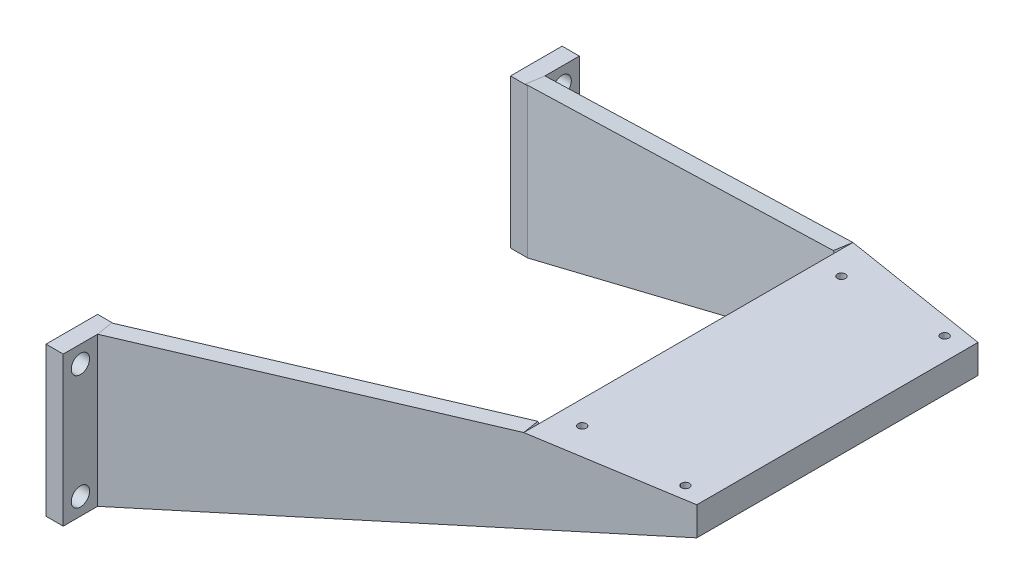
SolidWorks part; units mm, degrees
ref_plane "前视基准面" through (0, 0, 0) normal (0, 0, 1) x (1, 0, 0)
ref_plane "上视基准面" through (0, 0, 0) normal (0, 1, 0) x (1, 0, 0)
ref_plane "右视基准面" through (0, 0, 0) normal (1, 0, 0) x (0, 0, -1)
sketch "草图1" plane through (0, 0, 0) normal (1, 0, 0) x (0, 0, -1)
  line L0 (-2.8172, 6.9162) -> (-2.8172, -19.0838) construction
  line L1 (-5.8172, 6.9162) -> (0.1828, 6.9162)
  line L2 (-5.8172, 6.9162) -> (-5.8172, -19.0838)
  line L3 (-5.8172, -19.0838) -> (0.1828, -19.0838)
  line L4 (0.1828, 6.9162) -> (0.1828, -19.0838)
  line L5 (-44.8172, 16.944) -> (-44.8172, -30.3797) construction
  line L10 (-5.8172, 6.9162) -> (-5.8172, -19.0838)
  line L11 (0.1828, 6.9162) -> (0.1828, -19.0838)
  line L12 (-86.8172, 6.9162) -> (-86.8172, -19.0838) construction
  line L13 (-89.8172, 6.9162) -> (-89.8172, -19.0838)
  line L14 (-83.8172, 6.9162) -> (-83.8172, -19.0838)
  line L15 (-89.8172, 6.9162) -> (-89.8172, -19.0838)
  line L16 (-83.8172, -19.0838) -> (-89.8172, -19.0838)
  line L17 (-83.8172, 6.9162) -> (-83.8172, -19.0838)
  line L18 (-83.8172, 6.9162) -> (-89.8172, 6.9162)
  circle A0 centre (-2.8172, 3.9162) radius 1.6
  circle A1 centre (-2.8172, -16.0838) radius 1.6
  circle A2 centre (-86.8172, -16.0838) radius 1.6
  circle A3 centre (-86.8172, 3.9162) radius 1.6
  dimension "D2" = 3.2
  dimension "D3" = 3.2
  dimension "D1" = 20
  dimension "D4" = 6
  dimension "D5" = 3
  dimension "D6" = 3
  dimension "D7" = 42
extrude "凸台-拉伸1" add sketch "草图1" along normal blind 3 contours L4 L1 L2 L3 A1 A0 | L14 L18 L13 L16 A2 A3
ref_plane "基准面1" through (90, 0, 0) normal (-1, 0, 0) x (0, 0, 1)
sketch "草图10" plane through (3, 0, 0) normal (1, 0, 0) x (0, 0, -1)
  line L0 (-5.8172, -19.0838) -> (0.1828, -19.0838) construction
  line L1 (-5.8172, 6.9162) -> (-8.8172, 6.9162)
  line L2 (-5.8172, 6.9162) -> (-5.8172, -19.0838)
  line L3 (-5.8172, -19.0838) -> (-8.8172, -19.0838)
  line L4 (-8.8172, 6.9162) -> (-8.8172, -19.0838)
  dimension "D1" = 3
sketch "草图11" plane through (90, 0, 0) normal (-1, 0, 0) x (0, 0, 1)
  line L0 (5.8172, 6.9162) -> (8.8172, 6.9162) construction
  line L1 (19.8172, 18.9162) -> (22.8172, 18.9162)
  line L2 (19.8172, 18.9162) -> (19.8172, 8.9162)
  line L3 (19.8172, 8.9162) -> (22.8172, 8.9162)
  line L4 (22.8172, 18.9162) -> (22.8172, 8.9162)
  line L5 (8.8172, 6.9162) -> (8.8172, -19.0838) construction
  dimension "D1" = 12
  dimension "D2" = 11
  dimension "D3" = 10
  dimension "D4" = 3
loft "放样4" add profiles "草图11", "草图10"
sketch "草图12" plane through (3, 0, 0) normal (1, 0, 0) x (0, 0, -1)
  line L0 (-83.8172, -19.0838) -> (-89.8172, -19.0838) construction
  line L1 (-83.8172, 6.9162) -> (-80.8172, 6.9162)
  line L2 (-83.8172, 6.9162) -> (-83.8172, -19.0838)
  line L3 (-83.8172, -19.0838) -> (-80.8172, -19.0838)
  line L4 (-80.8172, 6.9162) -> (-80.8172, -19.0838)
  dimension "D1" = 3
sketch "草图13" plane through (90, 0, 0) normal (-1, 0, 0) x (0, 0, 1)
  line L0 (80.8172, 6.9162) -> (80.8172, -19.0838) construction
  line L1 (66.8172, 18.9162) -> (69.8172, 18.9162)
  line L2 (66.8172, 18.9162) -> (66.8172, 8.9162)
  line L3 (66.8172, 8.9162) -> (69.8172, 8.9162)
  line L4 (69.8172, 18.9162) -> (69.8172, 8.9162)
  line L5 (83.8172, 6.9162) -> (80.8172, 6.9162) construction
  dimension "D1" = 11
  dimension "D2" = 12
  dimension "D3" = 10
  dimension "D4" = 3
loft "放样5" add profiles "草图13", "草图12"
sketch "草图14" plane through (90, 0, 0) normal (1, 0, 0) x (0, 0, -1)
  line L1 (-69.8172, 18.9162) -> (-19.8172, 18.9162)
  line L2 (-69.8172, 18.9162) -> (-69.8172, 8.9162)
  line L3 (-69.8172, 8.9162) -> (-19.8172, 8.9162)
  line L4 (-19.8172, 18.9162) -> (-19.8172, 8.9162)
extrude "凸台-拉伸4" add sketch "草图14" along normal blind 3
sketch "草图15" plane through (13.2231, 0, 82.1721) normal (0.1589, 0, 0.9873) x (0.9873, 0, -0.1589)
  line L1 (68.9271, 24.583) -> (87.9519, 24.583)
  line L2 (68.9271, 24.583) -> (68.9271, 2.2776)
  line L3 (68.9271, 2.2776) -> (87.9519, 2.2776)
  line L4 (87.9519, 24.583) -> (87.9519, 2.2776)
extrude "切除-拉伸2" cut sketch "草图15" along normal blind 3
sketch "草图16" plane through (-0.8367, 0, 5.1998) normal (0.1589, 0, -0.9873) x (-0.9873, 0, -0.1589)
  line L1 (-86.3776, 22.7918) -> (-100.7289, 22.7918)
  line L2 (-86.3776, 22.7918) -> (-86.3776, 5.3541)
  line L3 (-86.3776, 5.3541) -> (-100.7289, 5.3541)
  line L4 (-100.7289, 22.7918) -> (-100.7289, 5.3541)
extrude "切除-拉伸3" cut sketch "草图16" along normal blind 3
sketch "草图17" plane through (3, 0, 0) normal (-1, 0, 0) x (0, 0, 1)
  line L0 (83.8172, -19.0838) -> (80.8172, -19.0838) construction
  line L1 (5.8172, 6.9162) -> (8.8172, 6.9162)
  line L2 (5.8172, 6.9162) -> (5.8172, -19.0838)
  line L3 (5.8172, -19.0838) -> (8.8172, -19.0838)
  line L4 (8.8172, 6.9162) -> (8.8172, -19.0838)
  line L5 (83.8172, 6.9162) -> (80.8172, 6.9162)
  line L6 (83.8172, 6.9162) -> (83.8172, -19.0838)
  line L7 (83.8172, -19.0838) -> (80.8172, -19.0838)
  line L8 (80.8172, 6.9162) -> (80.8172, -19.0838)
  line L9 (66.8172, 8.9162) -> (80.8172, -19.0838) construction
extrude "凸台-拉伸5" add sketch "草图17" along normal blind 3
sketch "草图18" plane through (0, 18.9162, 0) normal (0, 1, 0) x (1, 0, 0)
  line L0 (93, -69.3344) -> (67, -73.5183)
  line L1 (90, -69.8172) -> (3, -83.8172) construction
  line L2 (67, -73.5183) -> (67, -16.116)
  line L3 (90, -19.8172) -> (3, -5.8172) construction
  line L4 (67, -16.116) -> (93, -20.2999)
  line L5 (93, -20.2999) -> (93, -69.3344)
  dimension "D1" = 26
extrude "凸台-拉伸6" add sketch "草图18" against normal blind 3
sketch "草图19" plane through (13.2231, 0, 82.1721) normal (0.1589, 0, 0.9873) x (0.9873, 0, -0.1589)
  line L0 (-10.3546, 6.9162) -> (54.4687, 18.9162)
  line L1 (54.4687, 18.9162) -> (57.6431, 15.2006)
  line L3 (57.6431, 15.2006) -> (10.873, 4.0844)
  line L4 (10.873, 4.0844) -> (-10.3546, 6.9162)
extrude "凸台-拉伸10" add sketch "草图19" against normal up to vertex (2.9619 mm away)
sketch "草图20" plane through (-0.8367, 0, 5.1998) normal (0.1589, 0, -0.9873) x (-0.9873, 0, -0.1589)
  line L0 (-3.8861, 6.9162) -> (-68.7095, 18.9162)
  line L1 (-68.7095, 18.9162) -> (-71.5295, 14.9383)
  line L2 (-71.5295, 14.9383) -> (-30.1654, 5.8011)
  line L3 (-30.1654, 5.8011) -> (-3.8861, 6.9162)
extrude "凸台-拉伸11" add sketch "草图20" against normal up to vertex (2.9619 mm away)
sketch "草图21" plane through (0, 0, -0.1828) normal (0, 0, -1) x (-1, 0, 0)
  line L0 (-3, -19.0838) -> (-93, 13.9162)
  line L1 (-93, 18.9162) -> (-93, 8.9162) construction
  line L2 (-93, 13.9162) -> (-93, 8.9162)
  line L3 (-93, 8.9162) -> (-3, -19.0838)
  line L4 (-93, 18.9162) -> (-67, 18.9162) construction
  dimension "D1" = 5
extrude "切除-拉伸4" cut sketch "草图21" against normal blind 100
sketch "草图22" plane through (0, 15.9162, 0) normal (0, -1, 0) x (1, 0, 0)
  line L1 (67, 19.116) -> (70, 19.116)
  line L2 (67, 19.116) -> (67, 70.5183)
  line L3 (67, 70.5183) -> (70, 70.5183)
  line L4 (70, 19.116) -> (70, 70.5183)
  point P5 (0, 0)
  dimension "D1" = 3
extrude "凸台-拉伸12" add sketch "草图22" along normal blind 3
sketch "草图23" plane through (70, 0, 0) normal (1, 0, 0) x (0, 0, -1)
  line L0 (-19.5988, 12.9162) -> (-70.0356, 12.9162)
  line L1 (-19.5988, 15.9162) -> (-70.0356, 15.9162) construction
  arc A0 (-19.5988, 12.9162) -> (-70.0356, 12.9162) centre (-44.8172, -91.5783) ccw
extrude "切除-拉伸5" cut sketch "草图23" against normal blind 3
sketch "草图24" plane through (0, 18.9162, 0) normal (0, 1, 0) x (1, 0, 0)
  circle A0 centre (89.1, -67.4172) radius 0.7
  circle A1 centre (71.1, -67.4172) radius 0.7
  circle A2 centre (71.1, -22.2172) radius 0.7
  circle A3 centre (89.1, -22.2172) radius 0.7
  dimension "D1" = 1.4
  dimension "D2" = 1.4
  dimension "D3" = 1.4
  dimension "D4" = 1.4
extrude "切除-拉伸6" cut sketch "草图24" against normal blind 10
